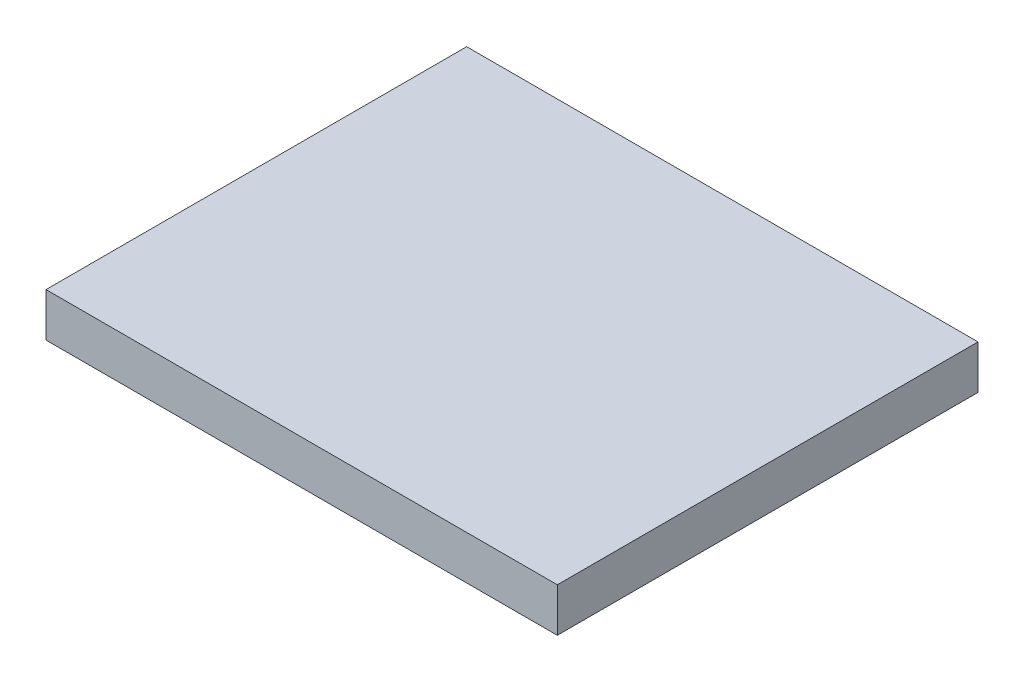
SolidWorks part; units mm, degrees
ref_plane "Front Plane" through (0, 0, 0) normal (0, 0, 1) x (1, 0, 0)
ref_plane "Top Plane" through (0, 0, 0) normal (0, 1, 0) x (1, 0, 0)
ref_plane "Right Plane" through (0, 0, 0) normal (1, 0, 0) x (0, 0, -1)
sketch "Sketch1" plane through (0, 0, 0) normal (0, 1, 0) x (1, 0, 0)
  line L1 (-51.1908, 26.8026) -> (65.6379, 26.8026)
  line L2 (-51.1908, 26.8026) -> (-51.1908, -69.3175)
  line L3 (-51.1908, -69.3175) -> (65.6379, -69.3175)
  line L4 (65.6379, 26.8026) -> (65.6379, -69.3175)
  dimension "D1" = 116.8286
  dimension "D2" = 96.12
extrude "Boss-Extrude1" add sketch "Sketch1" along normal blind 10
